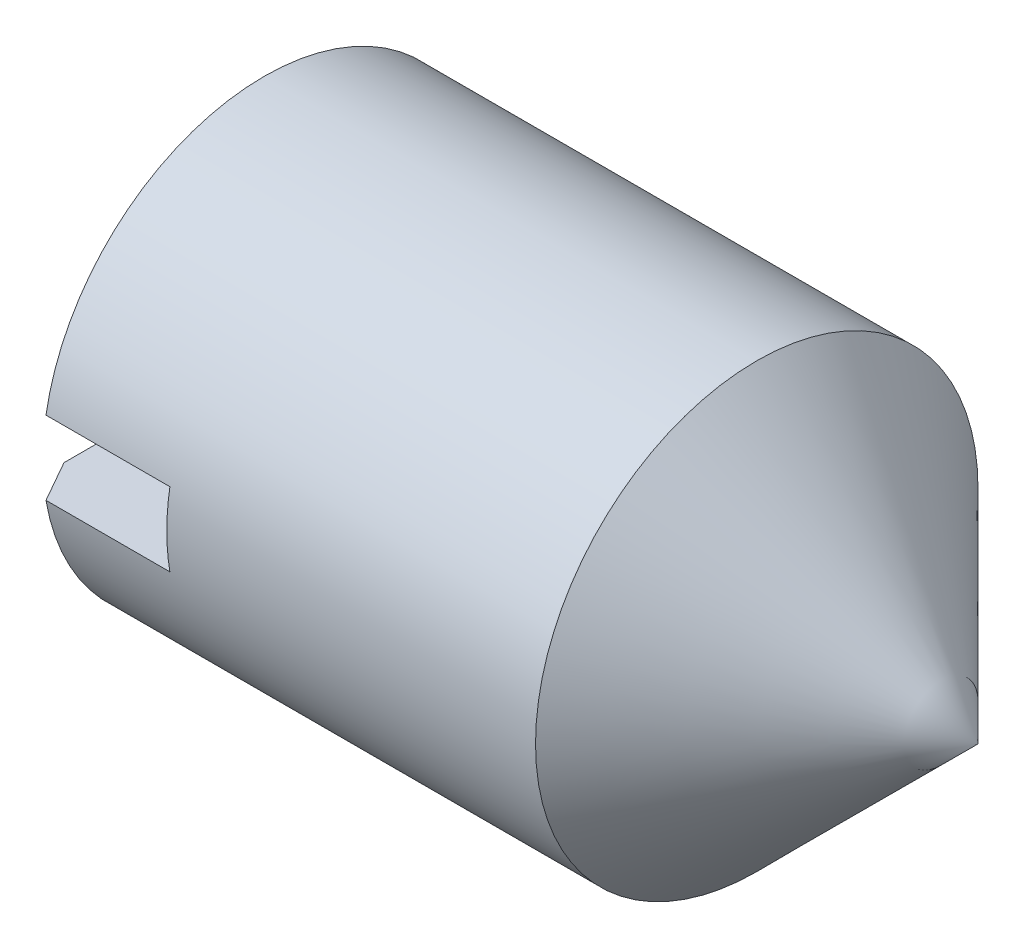
SolidWorks part; units mm, degrees
ref_plane "Plane1" through (0, 0, 0) normal (0, 0, 1) x (1, 0, 0)
ref_plane "Plane2" through (0, 0, 0) normal (0, 1, 0) x (1, 0, 0)
ref_plane "Plane3" through (0, 0, 0) normal (1, 0, 0) x (0, 0, -1)
sketch "BodySke" plane through (0, 0, 0) normal (0, 0, 1) x (1, 0, 0)
  line L0 (0, 0) -> (0, 2.4455)
  line L1 (0, 2.4455) -> (0.3201, 3)
  line L2 (0.3201, 3) -> (7, 3)
  line L3 (7, 3) -> (10, 0)
  line L4 (10, 0) -> (0, 0)
  line L5 (-12.7, 0) -> (88.9, 0) construction
  line L6 (7, -3) -> (10, 0) construction
  line L7 (0.5, 15.875) -> (0.5, -3.175) construction
  line L8 (0, -2.4455) -> (0.3201, -3) construction
  dimension "Cone_ang" = 90
  dimension "Length" = 10
  dimension "Diameter" = 6
  dimension "Drive_ch_ang" = 60
  dimension "Minor_dia" = 4.891
  dimension "Advance" = 1
revolve "BaseBody" add sketch "BodySke"
cosmetic thread "ThreadCosmetic" [suppressed]
extrude "Slot" cut sketch "Sketch2" against normal blind 2
sketch "Sketch2" plane through (0, 0, 0) normal (-1, 0, 0) x (0, 0, 1)
  line L0 (3, 0.5) -> (-3, 0.5)
  line L1 (3, -0.5) -> (3, 0.5)
  line L2 (-3, -0.5) -> (-3, 0.5)
  line L4 (3, -0.5) -> (-3, -0.5)
  circle A2 centre (0, 0) radius 3 construction
  dimension "D1" = 0.5
  dimension "Slot_width" = 1
sketch "ThdSchSke" plane through (0, 0, 0) normal (0, 0, 1) x (1, 0, 0)
  line L0 (0.3201, -2.4455) -> (-0.0681, -3)
  line L1 (0.3201, -2.4455) -> (0.7084, -3)
  line L2 (0.7084, -3) -> (0.7084, -3.75)
  line L3 (-3.175, 0) -> (5.1513, 0) construction
  line L4 (0.3201, 3) -> (0.3201, -3) construction
  line L5 (0.7084, -3.75) -> (-0.0681, -3.75)
  line L6 (-0.0681, -3.75) -> (-0.0681, -3)
  dimension "Thread_minor" = 4.891
  dimension "Diameter" = 6
  dimension "SideAngle" = 55
  dimension "VeeAngle" = 70
  dimension "Overcut" = 7.5
revolve "ThreadSchematic" [suppressed] cut sketch "ThdSchSke" angle 360 about L3
pattern_linear "ThdSchPat" [suppressed]
equation "\"Thread_minor@ThreadCosmetic\" = \"Minor_dia@BodySke\""
equation "\"Thread_minor@ThdSchSke\" = \"Thread_minor@ThreadCosmetic\""
equation "\"Diameter@ThdSchSke\" = \"Diameter@BodySke\""
equation "\"Overcut@ThdSchSke\" = \"Diameter@BodySke\" * 1.25"
equation "\"Num_threads@ThdSchPat\" = int( (\"Length@BodySke\" - ( ( ( \"Diameter@BodySke\" - \"Minor_dia@BodySke\" ) * 0.5 ) / tan( \"Drive_ch_ang@BodySke\" * 0.017453292 ) ) - ( ( \"Diameter@BodySke\" * 0.5 ) / tan( \"Cone_ang@BodySke\" * 0.008726646 ) ) ) / \"Advance@BodySke\" + 0.999 )  + 1"
equation "\"Advance@ThdSchPat\" = (\"Length@BodySke\" - ( ( ( \"Diameter@BodySke\" - \"Minor_dia@BodySke\" ) * 0.5 ) / tan( \"Drive_ch_ang@BodySke\" * 0.017453292 ) ) - ( ( \"Diameter@BodySke\" * 0.5 ) / tan( \"Cone_ang@BodySke\" * 0.008726646 ) ) ) /  (\"Num_threads@ThdSchPat\" - 1) 'relax it"
equation "' \"Num_threads@ThdSchPat\" = \"Num_threads@ThdSchPat\" - sgn( \"Num_threads@ThdSchPat\" - 1) '---chamfered tips only---"
equation "\"D1@Sketch2\" = \"Slot_width@Sketch2\" / 2"
